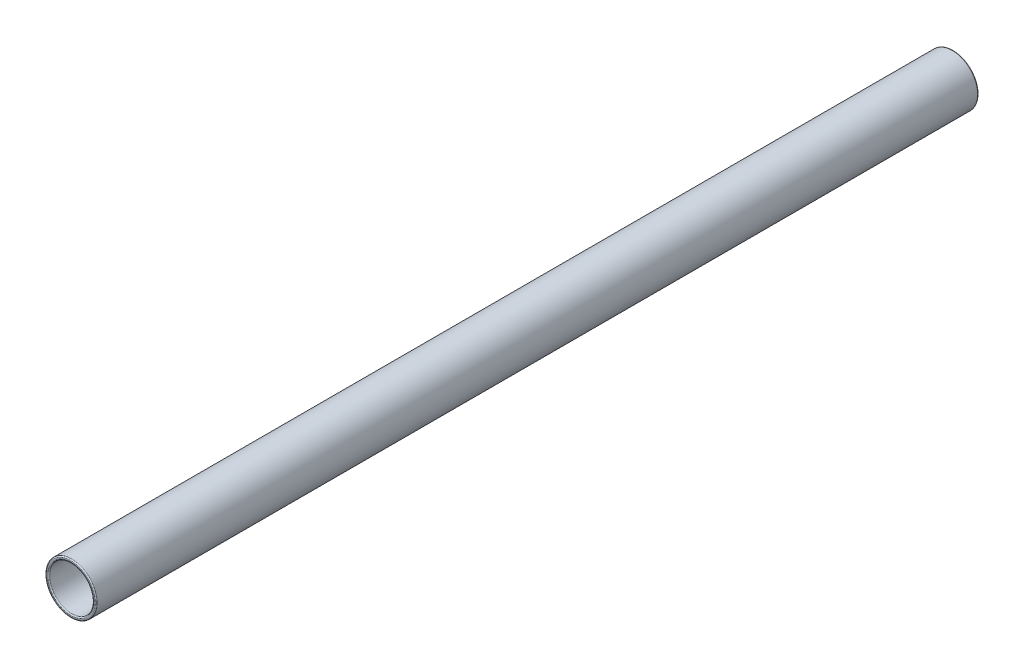
SolidWorks part; units mm, degrees
ref_plane "Front Plane" through (0, 0, 0) normal (0, 0, 1) x (1, 0, 0)
ref_plane "Top Plane" through (0, 0, 0) normal (0, 1, 0) x (1, 0, 0)
ref_plane "Right Plane" through (0, 0, 0) normal (1, 0, 0) x (0, 0, -1)
sketch "Sketch1" plane through (0, 0, 0) normal (0, 0, 1) x (1, 0, 0)
  circle A0 centre (0, 0) radius 11.5
  circle A1 centre (0, 0) radius 10
  dimension "D1" = 23
  dimension "D2" = 20
extrude "Boss-Extrude1" add sketch "Sketch1" along normal mid plane 400
fillet "Fillet1" radius 0.5 4 edges at (10, 0, -200) (11.5, 0, -200) (10, 0, 200) (11.5, 0, 200)
